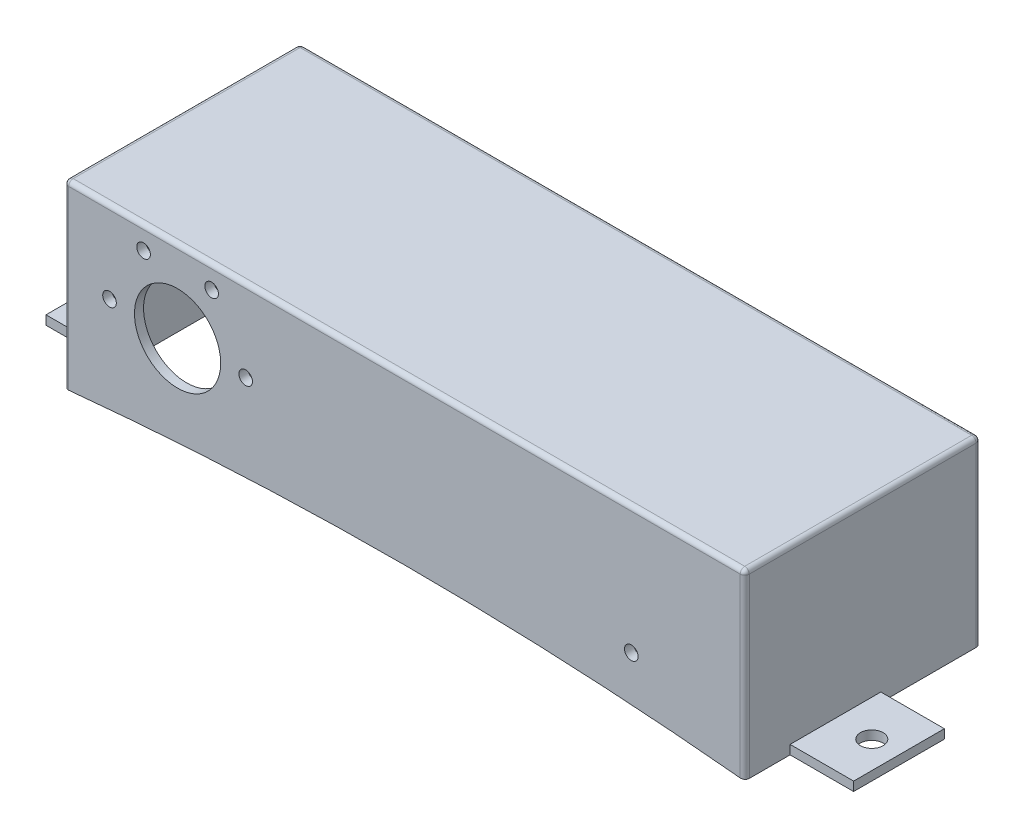
SolidWorks part; units mm, degrees
ref_plane "Front Plane" through (0, 0, 0) normal (0, 0, 1) x (1, 0, 0)
ref_plane "Top Plane" through (0, 0, 0) normal (0, 1, 0) x (1, 0, 0)
ref_plane "Right Plane" through (0, 0, 0) normal (1, 0, 0) x (0, 0, -1)
sketch "Sketch1" plane through (0, 0, 0) normal (0, 0, 1) x (1, 0, 0)
  line L0 (-65, 2) -> (-35, 2) construction
  line L1 (-75, -20) -> (75, -20)
  line L2 (-75, -20) -> (-75, 20)
  line L3 (-75, 20) -> (75, 20)
  line L4 (75, -20) -> (75, 20)
  line L5 (-75, -20) -> (75, 20) construction
  line L6 (-75, 20) -> (75, -20) construction
  circle A0 centre (-50, 2) radius 9.5
  arc A1 (-65, 2) -> (-35, 2) centre (-50, 2) cw construction
  circle A2 centre (-65, 2) radius 1.5
  circle A3 centre (-57.5, 14.9904) radius 1.5
  circle A4 centre (-42.5, 14.9904) radius 1.5
  circle A5 centre (-35, 2) radius 1.5
  circle A6 centre (50, -8) radius 1.5
  point P0 (0, 0)
  dimension "D1" = 19
  dimension "D7" = 3
  dimension "D12" = 3
  dimension "D2" = 150
  dimension "D3" = 40
  dimension "D4" = 22
  dimension "D5" = 25
  dimension "D6" = 30
  dimension "D9" = 12.9904
  dimension "D10" = 7.5
  dimension "D11" = 12.9904
  dimension "D13" = 12
  dimension "D14" = 25
  dimension "D8" = 4
extrude "Boss-Extrude1" add sketch "Sketch1" along normal blind 2
sketch "Sketch2" plane through (0, 0, 2) normal (0, 0, 1) x (1, 0, 0)
  line L0 (-73, -5) -> (-58, -5) construction
  line L1 (-62.5559, 7) -> (-45.1698, 7) construction
  line L2 (-45.1698, 7) -> (-12.0117, 7) construction
  line L3 (-37.6804, -5) -> (-5.2802, -5) construction
  line L4 (-75, -20) -> (75, -20) construction
  line L5 (-75, 20) -> (-75, -20) construction
  line L6 (25, -5) -> (65, -5)
  line L7 (65, -5) -> (40, -5) construction
  line L8 (75, -20) -> (75, 20) construction
  line L10 (75, 20) -> (-75, 20) construction
  line L11 (-73, -18) -> (73, -18)
  line L12 (-73, -18) -> (-73, 18)
  line L13 (-73, 18) -> (73, 18)
  line L14 (73, -18) -> (73, 18)
  line L15 (-73, -18) -> (73, 18) construction
  line L16 (-73, 18) -> (73, -18) construction
  line L18 (-75, -20) -> (75, -20)
  line L19 (-75, -20) -> (-75, 20)
  line L20 (-75, 20) -> (75, 20)
  line L21 (75, -20) -> (75, 20)
  line L22 (-75, -20) -> (75, 20) construction
  line L23 (-75, 20) -> (75, -20) construction
  text T0 "Disengaged" font "Century Gothic" height 1.5
  text T1 "        1" font "Century Gothic" height 1.5
  text T2 "   2" font "Century Gothic" height 1.5
  text T3 "    3" font "Century Gothic" height 1.5
  text T4 "Dead Mans Switch          " font "Century Gothic" height 1.5
  line M7 (75, -20) -> (75, 20)
  line M8 (75, 20) -> (-75, 20)
  line M9 (-75, 20) -> (-75, -20)
  line M10 (-75, -20) -> (75, -20)
  dimension "D1" = 15
  dimension "D2" = 27
  dimension "D3" = 2
  dimension "D4" = 12.4441
  dimension "D5" = 29.8302
  dimension "D6" = 37.3196
  dimension "D7" = 15
  dimension "D8" = 25
  dimension "D9" = 15
  dimension "D10" = 35
  dimension "D11" = 2
  dimension "D12" = 2
  dimension "D13" = 2
  dimension "D14" = 2
extrude "Boss-Extrude3" add sketch "Sketch2" against normal blind 50 contours L14 L11 L12 L13 M10 M7 M8 M9
sketch "Sketch3" plane through (0, 0, -48) normal (0, 0, -1) x (-1, 0, 0)
  line L1 (-75, -20) -> (75, -20)
  line L2 (-75, -20) -> (-75, 20)
  line L3 (-75, 20) -> (75, 20)
  line L4 (75, -20) -> (75, 20)
  line L5 (-75, -20) -> (75, 20) construction
  line L6 (-75, 20) -> (75, -20) construction
  point P0 (0, 0)
sketch "Sketch4" plane through (-75, 0, 0) normal (-1, 0, 0) x (0, 0, 1)
  line L0 (2, -20) -> (-48, -20) construction
  line L1 (-48, 20) -> (-48, -20) construction
  circle A0 centre (-38, -2) radius 5
  dimension "D1" = 10
  dimension "D2" = 18
  dimension "D3" = 10
extrude "Cut-Extrude1" cut sketch "Sketch4" against normal up to next
sketch "Sketch5" plane through (-75, 0, 0) normal (-1, 0, 0) x (0, 0, 1)
  line L0 (-48, -20) -> (-48, 20) construction
  line L1 (-48, 18) -> (-42, 18)
  line L2 (-48, 18) -> (-48, 12)
  line L3 (-48, 12) -> (-42, 12)
  line L4 (-42, 18) -> (-42, 12)
  line L5 (-45, 12) -> (-45, 18) construction
  line L6 (-48, 15) -> (-42, 15) construction
  line L7 (-48, 20) -> (-48, -20) construction
  line L8 (-48, -12) -> (-42, -12)
  line L9 (-48, -12) -> (-48, -18)
  line L10 (-48, -18) -> (-42, -18)
  line L11 (-42, -12) -> (-42, -18)
  line L12 (-45, -18) -> (-45, -12) construction
  line L13 (-48, -15) -> (-42, -15) construction
  line L14 (2, -20) -> (-48, -20) construction
  line L15 (2, 20) -> (-48, 20) construction
  circle A0 centre (-45, 15) radius 1.5
  circle A1 centre (-45, -15) radius 1.5
  point P96 (-45, 15)
  point P127 (-45, -15)
  dimension "D7" = 3
  dimension "D8" = 3
  dimension "D1" = 6
  dimension "D2" = 6
  dimension "D3" = 6
  dimension "D4" = 6
  dimension "D5" = 2
  dimension "D6" = 2
sketch "Sketch6" plane through (-75, 0, 0) normal (-1, 0, 0) x (0, 0, 1)
  line L0 (2, -20) -> (-48, -20) construction
  line L1 (2, 20) -> (2, -20) construction
  circle A0 centre (-23, -10) radius 3
  dimension "D1" = 6
  dimension "D2" = 10
  dimension "D3" = 25
sketch "Sketch8" plane through (0, 0, -48) normal (0, 0, -1) x (-1, 0, 0)
  line L0 (-75, -20) -> (75, -20) construction
  line L1 (-73, -18) -> (73, -18)
  line L2 (-73, -18) -> (-73, -20)
  line L3 (-73, -20) -> (73, -20)
  line L4 (73, -18) -> (73, -20)
  line L5 (0, -20) -> (0, -18) construction
  line L6 (-73, -19) -> (73, -19) construction
  point P656 (0, -19)
  dimension "D1" = 146
extrude "Cut-Extrude4" cut sketch "Sketch8" against normal blind 48
sketch "Sketch9" plane through (0, 20, 0) normal (0, 1, 0) x (1, 0, 0)
  line L0 (75, -2) -> (75, 48) construction
  line L1 (-75, 48) -> (75, 48)
  line L2 (-75, 48) -> (-75, 50)
  line L3 (-75, 50) -> (75, 50)
  line L4 (75, 48) -> (75, 50)
  line L5 (0, 50) -> (0, 48) construction
  line L6 (-75, 49) -> (75, 49) construction
  point P300 (0, 49)
  dimension "D1" = 2
extrude "Boss-Extrude4" add sketch "Sketch9" against normal blind 40
ref_plane "Plane1" through (0, 0, -18) normal (0, 0, 1) x (1, 0, 0)
sketch "Sketch10" plane through (0, 0, -18) normal (0, 0, 1) x (1, 0, 0)
  line L15 (0, -22) -> (0, 22) construction
  line L16 (-75, -20) -> (-89, -20)
  line L17 (-75, -20) -> (-75, -18)
  line L18 (-75, -18) -> (-89, -18)
  line L19 (-89, -20) -> (-89, -18)
  line L20 (-82, -18) -> (-82, -20) construction
  line L21 (-75, -19) -> (-89, -19) construction
  line L22 (75, -20) -> (75, -18)
  line L23 (75, -18) -> (89, -18)
  line L24 (89, -20) -> (89, -18)
  line L25 (75, -20) -> (89, -20)
  point P5 (0, 0)
  point P259 (-82, -19)
  dimension "D1" = 2
  dimension "D2" = 14
extrude "Boss-Extrude5" add sketch "Sketch10" along normal mid plane 20
sketch "Sketch11" plane through (0, 20, 0) normal (0, 1, 0) x (1, 0, 0)
  line L1 (-22, 18) -> (22, 18) construction
  line L2 (0, -22) -> (0, 22) construction
  line L3 (-89, 8) -> (-89, 28) construction
  circle A0 centre (-83, 18) radius 2.5
  circle A1 centre (83, 18) radius 2.5
  dimension "D1" = 5
  dimension "D2" = 6
  dimension "D3" = 0
extrude "Cut-Extrude5" cut sketch "Sketch11" against normal through all
sketch "Sketch12" plane through (0, 0, -50) normal (0, 0, -1) x (-1, 0, 0)
  line L0 (-59.8547, -0.5124) -> (-45.1499, -0.5124)
  line L1 (-52.5023, -19.5509) -> (-52.5023, -7.0009) construction
  line L2 (-59.2322, -11.1119) -> (-45.7725, -11.1119)
  line L3 (-42.9523, -0.5124) -> (-42.9523, -18.5852) construction
  line L4 (-62.0523, -0.5124) -> (-62.0523, -13.995) construction
  line L5 (-43.1587, -2.7003) -> (-43.7813, -9.2997)
  line L6 (-61.8459, -2.7003) -> (-61.2233, -9.2997)
  line L7 (-62.0523, -0.5124) -> (-62.0523, 0.0237) construction
  line L8 (-65.0046, -6) -> (-40, -6) construction
  line L9 (-26.8459, -2.7003) -> (-26.2233, -9.2997)
  line L10 (-24.2322, -11.1119) -> (-10.7725, -11.1119)
  line L11 (-24.8547, -0.5124) -> (-10.1499, -0.5124)
  line L12 (-8.1587, -2.7003) -> (-8.7813, -9.2997)
  line L14 (-5, -6) -> (5, -6) construction
  arc A0 (-43.7813, -9.2997) -> (-45.7725, -11.1119) centre (-45.7725, -9.1119) cw
  arc A1 (-59.2322, -11.1119) -> (-61.2233, -9.2997) centre (-59.2322, -9.1119) cw
  arc A2 (-43.1587, -2.7003) -> (-45.1499, -0.5124) centre (-45.1499, -2.5124) ccw
  arc A3 (-61.8459, -2.7003) -> (-59.8547, -0.5124) centre (-59.8547, -2.5124) cw
  circle A4 centre (-65.0046, -6) radius 1.5
  circle A5 centre (-40, -6) radius 1.5
  arc A6 (-24.2322, -11.1119) -> (-26.2233, -9.2997) centre (-24.2322, -9.1119) cw
  arc A7 (-26.8459, -2.7003) -> (-24.8547, -0.5124) centre (-24.8547, -2.5124) cw
  arc A8 (-8.1587, -2.7003) -> (-10.1499, -0.5124) centre (-10.1499, -2.5124) ccw
  arc A9 (-8.7813, -9.2997) -> (-10.7725, -11.1119) centre (-10.7725, -9.1119) cw
  circle A10 centre (-5, -6) radius 1.5
  circle A11 centre (-30.0046, -6) radius 1.5
  circle A12 centre (5, -6) radius 4
  point P4 (-52.5023, -0.5124)
  point P8 (-61.5346, -6)
  point P10 (-43.47, -6)
  dimension "D1" = 2
  dimension "D3" = 3
  dimension "D7" = 3
  dimension "D11" = 40
  dimension "D15" = 8
  dimension "D2" = 7.3524
  dimension "D4" = 3.47
  dimension "D5" = 3.47
  dimension "D6" = 10.5994
  dimension "D8" = 25.0046
  dimension "D9" = 1.0009
  dimension "D10" = 4.111
  dimension "D12" = 6
  dimension "D14" = 9.9954
  dimension "D16" = 10
  dimension "D13" = 2
extrude "Cut-Extrude6" cut sketch "Sketch12" against normal blind 2
sketch "Sketch14" plane through (0, 0, -50) normal (0, 0, -1) x (-1, 0, 0)
  line L1 (-75, -20) -> (75, -20)
  arc A0 (-75, -20) -> (75, -20) centre (0, -766.2406) cw
  dimension "D1" = 750
extrude "Cut-Extrude7" cut sketch "Sketch14" against normal blind 60
fillet "Fillet1" radius 1 8 edges at (-75, 0, -50) (-75, 20, -24) (-75, 0, 2) (75, 0, -50) (0, 20, -50) (0, 20, 2) (75, 0, 2) (75, 20, -24)
